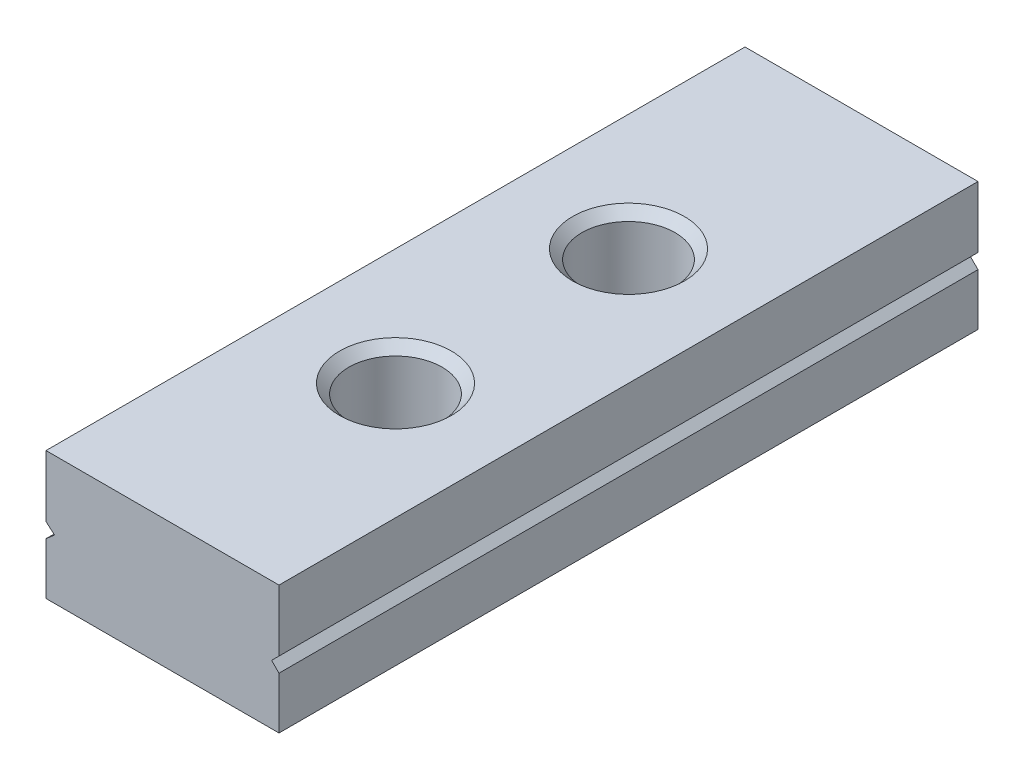
SolidWorks part; units mm, degrees
ref_plane "前视基准面" through (0, 0, 0) normal (0, 0, 1) x (1, 0, 0)
ref_plane "上视基准面" through (0, 0, 0) normal (0, 1, 0) x (1, 0, 0)
ref_plane "右视基准面" through (0, 0, 0) normal (1, 0, 0) x (0, 0, -1)
sketch "草图1" plane through (0, 0, 0) normal (0, 1, 0) x (1, 0, 0)
  line L1 (0, 0) -> (5, 0)
  line L2 (0, 0) -> (0, -15)
  line L3 (0, -15) -> (5, -15)
  line L4 (5, 0) -> (5, -15)
  dimension "D1" = 5
  dimension "D2" = 15
extrude "凸台-拉伸1" add sketch "草图1" along normal blind 2.75
sketch "草图2" plane through (0, 0, 0) normal (0, -1, 0) x (-1, 0, 0)
  line L0 (-2.5, -15) -> (-2.5, -10) construction
  line L1 (0, -15) -> (-5, -15) construction
  line L2 (-2.5, 0) -> (-2.5, -5) construction
  line L3 (-5, 0) -> (0, 0) construction
  circle A0 centre (-2.5, -10) radius 1
  circle A1 centre (-2.5, -5) radius 1
  dimension "D2" = 2
  dimension "D1" = 5
extrude "切除-拉伸1" cut sketch "草图2" against normal through all
sketch "草图3" plane through (0, 0, 0) normal (0, 0, -1) x (-1, 0, 0)
  line L0 (0, 1.1122) -> (-0.1834, 1.2712)
  line L1 (0, 2.75) -> (0, 0) construction
  line L2 (-0.1834, 1.2712) -> (0, 1.4302)
  line L3 (-5, 1.1122) -> (-4.841, 1.2712)
  line L4 (-5, 2.75) -> (-5, 0) construction
  line L5 (-4.841, 1.2712) -> (-5, 1.4302)
  line L6 (0, 1.1122) -> (0, 1.4302)
  line L7 (-5, 1.1122) -> (-5, 1.4302)
extrude "切除-拉伸2" cut sketch "草图3" against normal through all
chamfer "倒角1" distance 0.2 angle 45 2 edges at (2.5, 2.75, 4) (2.5, 2.75, 9)
